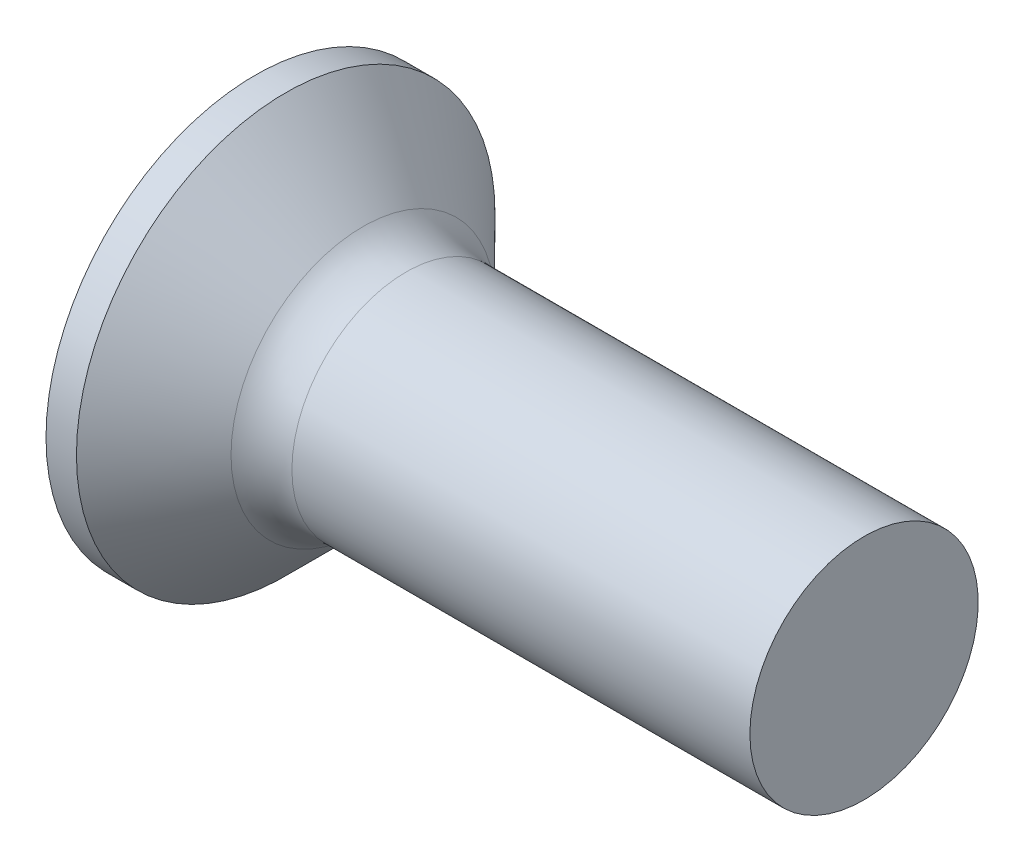
SolidWorks part; units mm, degrees
revolve "Base-Revolve" add sketch "BodySke"
sketch "BodySke" plane through (0, 0, 0) normal (0, 0, 1) x (1, 0, 0)
  line L0 (0, 0) -> (0, 2.75)
  line L1 (0, 2.75) -> (0.4, 2.75)
  line L2 (1.65, 1.5) -> (8, 1.5)
  line L3 (8, 1.5) -> (8, 0)
  line L4 (8, 0) -> (0, 0)
  line L5 (-6.35, 0) -> (82.55, 0) construction
  line L6 (1.65, -1.5) -> (8, -1.5) construction
  line L7 (0.4, -2.75) -> (1.65, -1.5) construction
  line L8 (0.4, 2.75) -> (1.65, 1.5)
  line L9 (0, -2.75) -> (0.4, -2.75) construction
  line L10 (2.15, 3.0875) -> (2.15, -6.4375) construction
  line L11 (0, 6.35) -> (0, -3.175) construction
  dimension "Diameter" = 3
  dimension "Length" = 8
  dimension "Head_ht" = 1.65
  dimension "Head_dia" = 5.5
  dimension "Head_ang" = 90
  dimension "D6" = 0.4
  dimension "Advance" = 0.5
  dimension "Thread_nom" = 8
cosmetic thread "ThreadCosmetic" [suppressed]
fillet "Fillet1" radius 0.8 1 edges at (1.65, 0, 1.5)
ref_plane "Plane1" through (0, 0, 0) normal (0, 0, 1) x (1, 0, 0)
ref_plane "Plane2" through (0, 0, 0) normal (0, 1, 0) x (1, 0, 0)
ref_plane "Plane3" through (0, 0, 0) normal (1, 0, 0) x (0, 0, -1)
sketch "Sketch3" plane through (0, 0, 0) normal (-1, 0, 0) x (0, 0, 1)
  line L0 (-0.37, 1.5) -> (0.37, 1.5)
  line L1 (0.37, 1.5) -> (0.37, -1.5)
  line L2 (0.37, -1.5) -> (-0.37, -1.5)
  line L3 (-0.37, -1.5) -> (-0.37, 1.5)
  dimension "Cross_dia" = 3
  dimension "Cross_width" = 0.74
  dimension "D1" = 1.5
  dimension "D2" = 0.37
ref_plane "Plane4" through (2.01, 0, 0) normal (-1, 0, 0) x (0, 0, 1)
sketch "Sketch4" plane through (2.01, 0, 0) normal (-1, 0, 0) x (0, 0, 1)
  line L0 (-0.37, 0.4979) -> (0.37, 0.4979)
  line L3 (0.37, 0.4979) -> (0.37, -0.4979)
  line L4 (0.37, -0.4979) -> (-0.37, -0.4979)
  line L5 (-0.37, -0.4979) -> (-0.37, 0.4979)
  dimension "D2" = 0.9957
  dimension "D1" = 0.74
  dimension "D4" = 0.4979
  dimension "D3" = 0.37
loft "Recess" cut profiles "Sketch3", "Sketch4"
pattern_circular "RecPat" count 2 every 90 about axis through (0, 0, 0) along (1, 0, 0) of "Recess"
sketch "RecCorSke" plane through (0, 0, 0) normal (0, 0, 1) x (1, 0, 0)
  line L0 (-3.175, 0) -> (15.875, 0) construction
  line L2 (0, 0) -> (0, 0.6966)
  line L3 (0, 0.6966) -> (2.01, 0.556)
  line L4 (2.01, 0.556) -> (2.1907, 0)
  line L5 (2.1907, 0) -> (0, 0)
  dimension "Diameter" = 1.112
  dimension "Depth" = 2.01
  dimension "Draft_angle" = 4
  dimension "Bottom_angle" = 18
revolve "RecessCore" cut sketch "RecCorSke" angle 360 about L0
sketch "ThdSchSke" plane through (0, 0, 0) normal (0, 0, 1) x (1, 0, 0)
  line L0 (2.15, -1.2195) -> (1.9536, -1.5)
  line L1 (2.15, -1.2195) -> (2.3464, -1.5)
  line L2 (2.3464, -1.5) -> (2.3464, -1.875)
  line L3 (-3.175, 0) -> (5.1513, 0) construction
  line L5 (2.3464, -1.875) -> (1.9536, -1.875)
  line L6 (1.9536, -1.875) -> (1.9536, -1.5)
  line L7 (0, 2.75) -> (0, -2.75) construction
  dimension "Diameter" = 3
  dimension "Thread_minor" = 2.439
  dimension "Start" = 2.15
revolve "ThreadSchematic" [suppressed] cut sketch "ThdSchSke" angle 360 about L3
pattern_linear "ThdSchPat" [suppressed]
equation "\"D1@Sketch3\" = \"Cross_dia@Sketch3\" / 2"
equation "\"D2@Sketch3\" = \"Cross_width@Sketch3\" / 2"
equation "\"Depth@RecCorSke\" = \"Cross_depth@Plane4\""
equation "\"D1@Sketch4\" = \"Cross_width@Sketch3\""
equation "\"D2@Sketch4\" = \"Cross_dia@Sketch3\" - 2.0 * \"Cross_depth@Plane4\" * tan(26.5  * 0.017453292)"
equation "\"D3@Sketch4\" = \"D1@Sketch4\" / 2"
equation "\"D4@Sketch4\" = \"D2@Sketch4\" / 2"
equation "\"Thread_length@ThreadCosmetic\" = ((sgn( (\"Length@BodySke\" - \"Advance@BodySke\" * 1.0 - \"Head_ht@BodySke\" ) - \"Thread_nom@BodySke\" )-1)*( (\"Length@BodySke\" - \"Advance@BodySke\" * 1.0 - \"Head_ht@BodySke\" ) - \"Thread_nom@BodySke\" ))/-2+ \"Thread_nom@BodySke\""
equation "\"Thread_minor@ThdSchSke\" = \"Thread_minor@ThreadCosmetic\""
equation "\"Diameter@ThdSchSke\" = \"Diameter@BodySke\""
equation "\"Overcut@ThdSchSke\" = \"Diameter@BodySke\" * 1.25"
equation "\"Start@ThdSchSke\" = 0.000001 + \"Length@BodySke\" - \"Thread_length@ThreadCosmetic\"  '---Countersunk---"
equation "\"Num_threads@ThdSchPat\" = int( \"Thread_length@ThreadCosmetic\" / \"Advance@BodySke\" + 0.999 )  + 1"
equation "\"Advance@ThdSchPat\" = \"Thread_length@ThreadCosmetic\" /  (\"Num_threads@ThdSchPat\" - 1) 'relax it"
